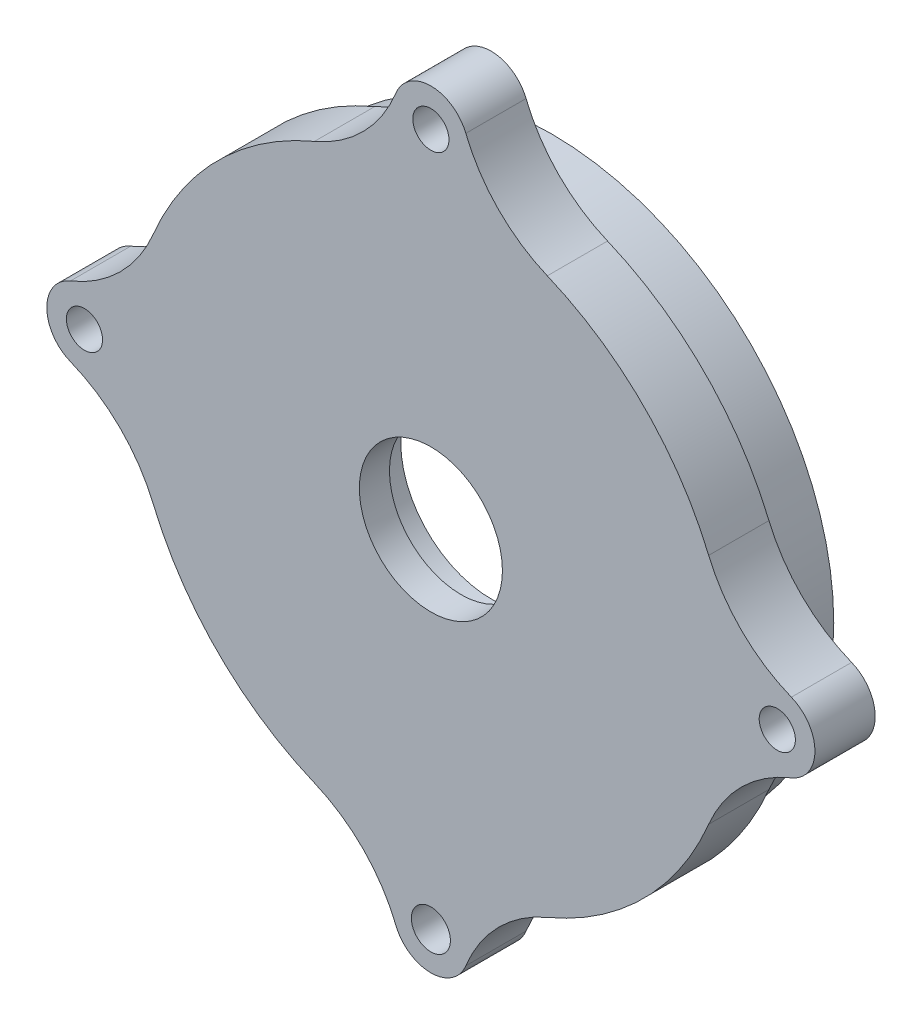
SolidWorks part; units mm, degrees
ref_plane "前视基准面" through (0, 0, 0) normal (0, 0, 1) x (1, 0, 0)
ref_plane "上视基准面" through (0, 0, 0) normal (0, 1, 0) x (1, 0, 0)
ref_plane "右视基准面" through (0, 0, 0) normal (1, 0, 0) x (0, 0, -1)
sketch "草图1" plane through (0, 0, 0) normal (0, 0, 1) x (1, 0, 0)
  circle A0 centre (0, 0) radius 20
  dimension "D1" = 40
extrude "凸台-拉伸1" add sketch "草图1" along normal blind 4
sketch "草图2" plane through (0, 0, 0) normal (0, 0, -1) x (-1, 0, 0)
  circle A0 centre (0, 0) radius 6
  dimension "D1" = 12
extrude "切除-拉伸1" cut sketch "草图2" against normal blind 2
sketch "草图3" plane through (0, 0, 4) normal (0, 0, 1) x (1, 0, 0)
  circle A0 centre (0, 0) radius 4.75
  dimension "D1" = 9.5
extrude "切除-拉伸2" cut sketch "草图3" against normal blind 22
sketch "草图4" plane through (0, 0, 0) normal (0, 0, -1) x (-1, 0, 0)
  circle A0 centre (0, 0) radius 17.5
  circle A1 centre (0, 0) radius 18.75
  dimension "D1" = 37.5
  dimension "D2" = 35
extrude "凸台-拉伸2" add sketch "草图4" along normal blind 4
sketch "草图5" plane through (0, 0, 4) normal (0, 0, 1) x (1, 0, 0)
  arc A0 (-2.3191, -23.9337) -> (2.3191, -23.9337) centre (0, -23) ccw
  arc A1 (7.7303, -18.4457) -> (2.3191, -23.9337) centre (11.5955, -27.6685) ccw
  arc A2 (-7.7303, -18.4457) -> (7.7303, -18.4457) centre (0, 0) ccw
  arc A3 (-2.3191, -23.9337) -> (-7.7303, -18.4457) centre (-11.5955, -27.6685) ccw
  arc A4 (-23.9337, 2.3191) -> (-23.9337, -2.3191) centre (-23, 0) ccw
  arc A5 (-18.4457, -7.7303) -> (-23.9337, -2.3191) centre (-27.6685, -11.5955) ccw
  arc A6 (-18.4457, 7.7303) -> (-18.4457, -7.7303) centre (0, 0) ccw
  arc A7 (-23.9337, 2.3191) -> (-18.4457, 7.7303) centre (-27.6685, 11.5955) ccw
  arc A8 (23.9337, -2.3191) -> (23.9337, 2.3191) centre (23, 0) ccw
  arc A9 (18.4457, 7.7303) -> (23.9337, 2.3191) centre (27.6685, 11.5955) ccw
  arc A10 (18.4457, -7.7303) -> (18.4457, 7.7303) centre (0, 0) ccw
  arc A11 (23.9337, -2.3191) -> (18.4457, -7.7303) centre (27.6685, -11.5955) ccw
  arc A12 (2.3191, 23.9337) -> (-2.3191, 23.9337) centre (0, 23) ccw
  arc A13 (-7.7303, 18.4457) -> (-2.3191, 23.9337) centre (-11.5955, 27.6685) ccw
  arc A14 (7.7303, 18.4457) -> (-7.7303, 18.4457) centre (0, 0) ccw
  arc A15 (2.3191, 23.9337) -> (7.7303, 18.4457) centre (11.5955, 27.6685) ccw
  circle A16 centre (0, 23) radius 1.2
  circle A17 centre (23, 0) radius 1.2
  circle A18 centre (0, -23) radius 1.2949
  circle A19 centre (-23, 0) radius 1.2
extrude "凸台-拉伸3" add sketch "草图5" against normal blind 4
